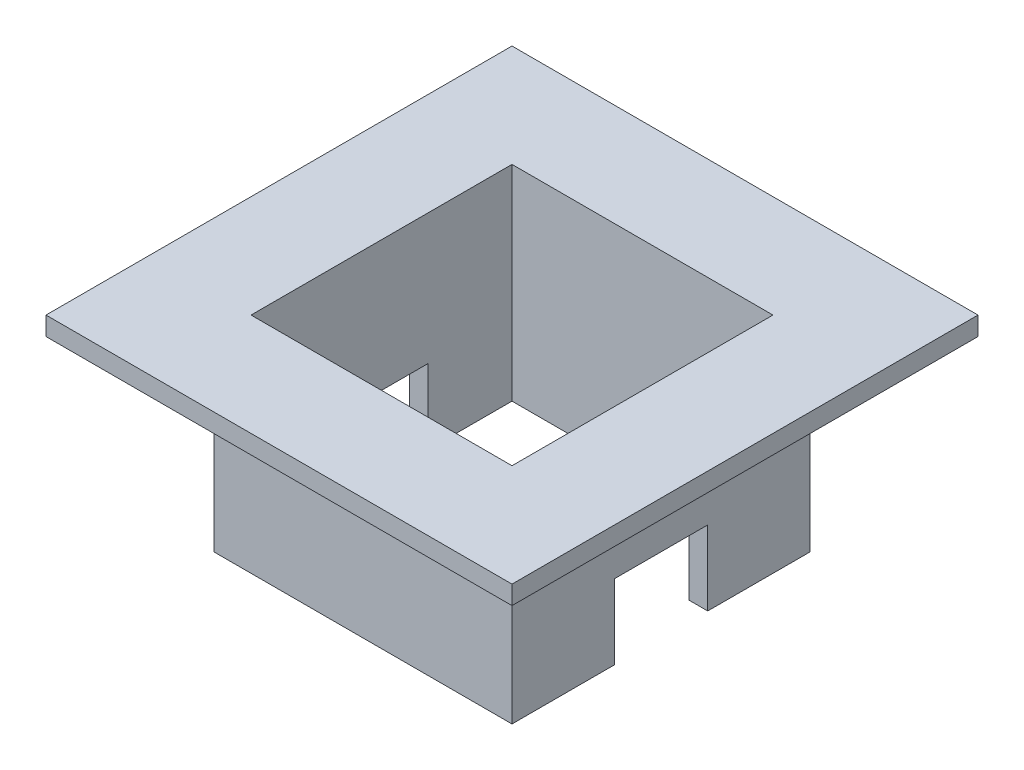
SolidWorks part; units mm, degrees
ref_plane "Front Plane" through (0, 0, 0) normal (0, 0, 1) x (1, 0, 0)
ref_plane "Top Plane" through (0, 0, 0) normal (0, 1, 0) x (1, 0, 0)
ref_plane "Right Plane" through (0, 0, 0) normal (1, 0, 0) x (0, 0, -1)
sketch "Sketch1" plane through (0, 0, 0) normal (0, 1, 0) x (1, 0, 0)
  line L0 (-16, -16) -> (-16, 16)
  line L1 (14, -14) -> (-14, -14)
  line L2 (14, -14) -> (14, 14)
  line L3 (14, 14) -> (-14, 14)
  line L4 (-14, -14) -> (-14, 14)
  line L5 (14, -14) -> (-14, 14) construction
  line L6 (14, 14) -> (-14, -14) construction
  line L7 (16, 16) -> (-16, 16)
  line L8 (16, -16) -> (16, 16)
  line L9 (16, -16) -> (-16, -16)
  point P0 (0, 0)
  dimension "D1" = 28
  dimension "D2" = 2
extrude "Boss-Extrude1" add sketch "Sketch1" along normal blind 20
sketch "Sketch2" plane through (16, 0, 0) normal (1, 0, 0) x (0, 0, -1)
  line L0 (-16, 0) -> (16, 0) construction
  line L1 (5, 8) -> (-5, 8)
  line L2 (5, 8) -> (5, 0)
  line L3 (5, 0) -> (-5, 0)
  line L4 (-5, 8) -> (-5, 0)
  line L5 (5, 8) -> (-5, 0) construction
  line L6 (5, 0) -> (-5, 8) construction
  line L7 (0, 4) -> (0, 0) construction
  point P0 (0, 4)
  dimension "D1" = 8
  dimension "D2" = 10
extrude "Cut-Extrude1" cut sketch "Sketch2" against normal through all
sketch "Sketch3" plane through (0, 20, 0) normal (0, 1, 0) x (1, 0, 0)
  line L1 (-25, -25) -> (25, -25)
  line L2 (-25, -25) -> (-25, 25)
  line L3 (-25, 25) -> (25, 25)
  line L4 (25, -25) -> (25, 25)
  line L5 (-25, -25) -> (25, 25) construction
  line L6 (-25, 25) -> (25, -25) construction
  line L7 (-14, -14) -> (14, -14)
  line L8 (-14, -14) -> (-14, 14)
  line L9 (-14, 14) -> (14, 14)
  line L10 (14, -14) -> (14, 14)
  line L11 (-14, -14) -> (14, 14) construction
  line L12 (-14, 14) -> (14, -14) construction
  point P0 (0, 0)
  point P6 (0, 0)
  dimension "D1" = 50
extrude "Boss-Extrude2" add sketch "Sketch3" along normal blind 2
